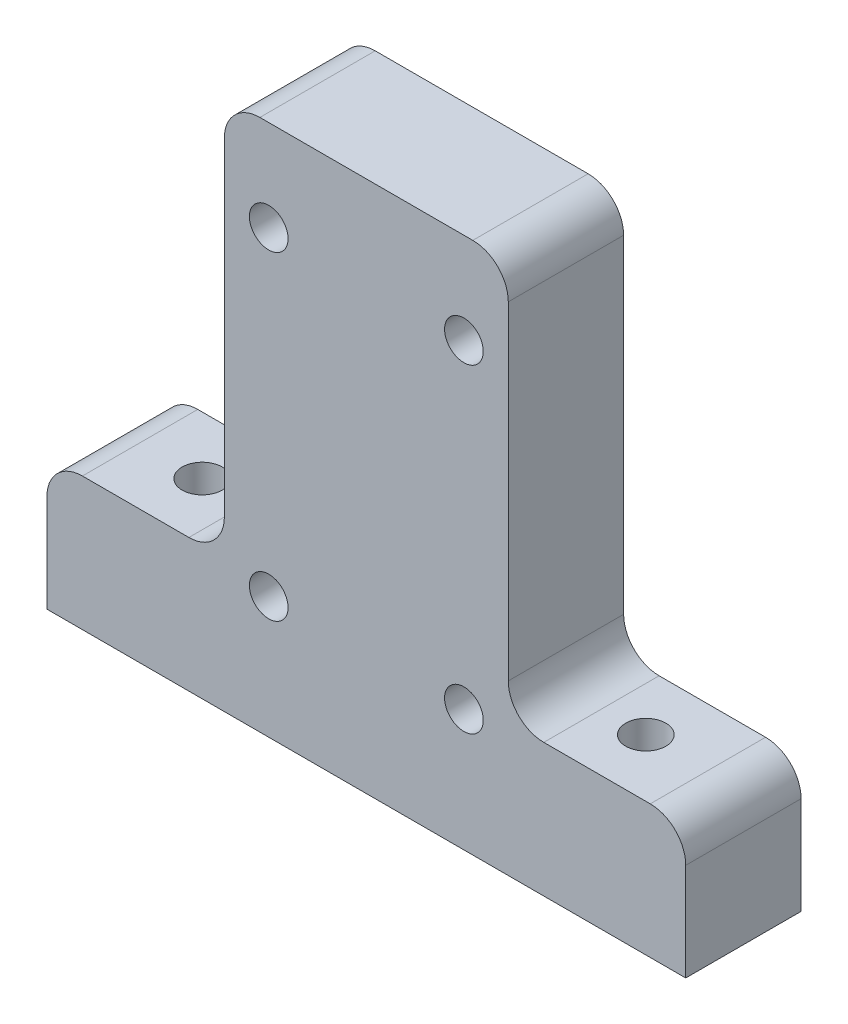
SolidWorks part; units mm, degrees
ref_plane "Front Plane" through (0, 0, 0) normal (0, 0, 1) x (1, 0, 0)
ref_plane "Top Plane" through (0, 0, 0) normal (0, 1, 0) x (1, 0, 0)
ref_plane "Right Plane" through (0, 0, 0) normal (1, 0, 0) x (0, 0, -1)
sketch "Sketch1" plane through (0, 0, 0) normal (0, 0, 1) x (1, 0, 0)
  line L1 (0, 0) -> (16, 0)
  line L2 (0, 0) -> (0, 30)
  line L3 (0, 30) -> (16, 30)
  line L4 (16, 0) -> (16, 30)
  dimension "D1" = 30
  dimension "D2" = 16
extrude "Boss-Extrude1" add sketch "Sketch1" along normal blind 6.5
sketch "Sketch3" plane through (0, 0, 0) normal (0, 0, -1) x (-1, 0, 0)
  line L0 (-13.5, 6.87) -> (-2.5, 6.87) construction
  line L1 (0, 0) -> (-16, 0) construction
  circle A0 centre (-13.5, 6.87) radius 1.09
  circle A1 centre (-2.5, 6.87) radius 1.09
  circle A2 centre (-2.5, 24.87) radius 1.09
  circle A3 centre (-13.5, 24.87) radius 1.09
  point P8 (-8, 6.87)
  point P11 (-8, 0)
  dimension "D1" = 2.18
  dimension "D2" = 11
  dimension "D3" = 18
  dimension "D4" = 6.87
extrude "Cut-Extrude1" cut sketch "Sketch3" against normal through all
fillet "Fillet1" radius 2 2 edges at (16, 30, 3.25) (0, 30, 3.25)
sketch "Sketch4" plane through (0, 0, 0) normal (0, -1, 0) x (1, 0, 0)
  line L0 (20.5, 3.25) -> (-4.5, 3.25) construction
  line L3 (0, 0) -> (16, 0) construction
  line L6 (16, 6.5) -> (16, 0) construction
  circle A0 centre (20.5, 3.25) radius 1.13
  circle A1 centre (-4.5, 3.25) radius 1.13
  point P4 (8, 3.25)
  point P7 (8, 0)
  point P10 (16, 3.25)
  dimension "D1" = 2.26
  dimension "D2" = 25
ref_plane "center plane" through (8, 0, 0) normal (1, 0, 0) x (0, 0, -1)
sketch "Sketch5" plane through (0, 0, 6.5) normal (0, 0, 1) x (1, 0, 0)
  line L0 (0, 28) -> (0, 0) construction
  line L1 (0, 7.5) -> (-10, 7.5)
  line L2 (0, 7.5) -> (0, 0)
  line L3 (0, 0) -> (-10, 0)
  line L4 (-10, 7.5) -> (-10, 0)
  line L5 (8, 0) -> (8, -3.9468) construction
  line L6 (8, -3.575) -> (8, 3.575) construction
  line L7 (26, 7.5) -> (26, 0)
  line L8 (16, 0) -> (26, 0)
  line L9 (16, 7.5) -> (16, 0)
  line L10 (16, 7.5) -> (26, 7.5)
  dimension "D1" = 10
  dimension "D2" = 7.5
extrude "Boss-Extrude2" add sketch "Sketch5" against normal up to surface (6.5 mm away) up to face at (1.41, 6.87, 0)
fillet "Fillet2" radius 2 2 edges at (16, 7.5, 3.25) (0, 7.5, 3.25)
fillet "Fillet3" radius 2 1 edges at (26, 7.5, 3.25)
fillet "Fillet4" radius 2 1 edges at (-10, 7.5, 3.25)
extrude "Cut-Extrude2" cut sketch "Sketch4" against normal through all
